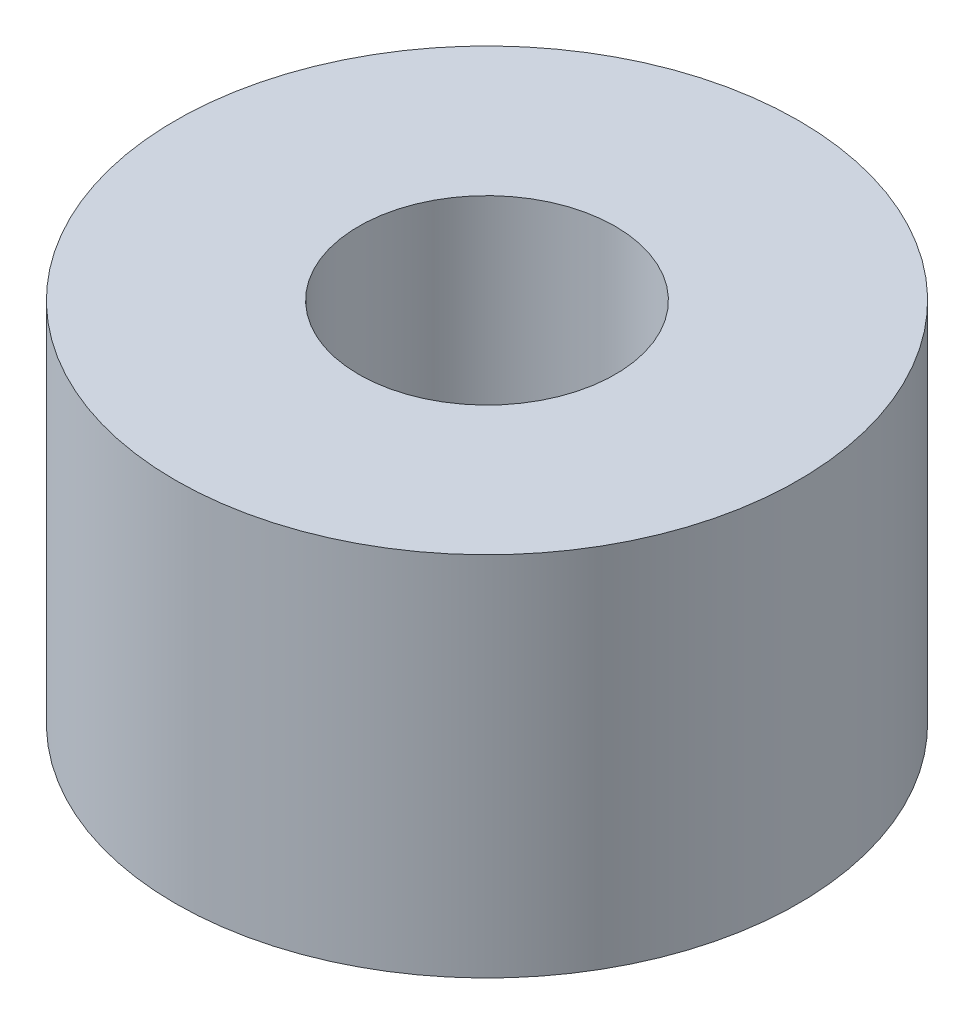
SolidWorks part; units mm, degrees
ref_plane "Front Plane" through (0, 0, 0) normal (0, 0, 1) x (1, 0, 0)
ref_plane "Top Plane" through (0, 0, 0) normal (0, 1, 0) x (1, 0, 0)
ref_plane "Right Plane" through (0, 0, 0) normal (1, 0, 0) x (0, 0, -1)
sketch "Sketch1" plane through (0, 0, 0) normal (0, 1, 0) x (1, 0, 0)
  circle A0 centre (0, 0) radius 1.05
  circle A1 centre (0, 0) radius 2.55
  dimension "D1" = 2.1
  dimension "D2" = 5.1
extrude "Boss-Extrude1" add sketch "Sketch1" along normal blind 3
